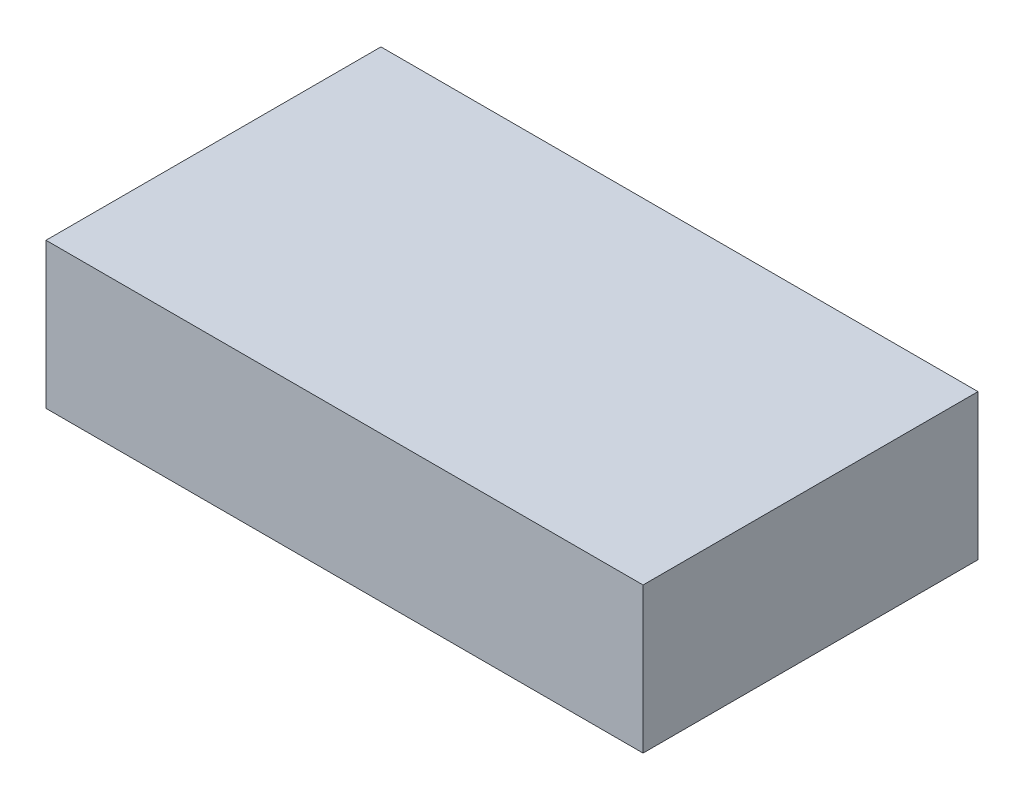
SolidWorks part; units mm, degrees
ref_plane "Front Plane" through (0, 0, 0) normal (0, 0, 1) x (1, 0, 0)
ref_plane "Top Plane" through (0, 0, 0) normal (0, 1, 0) x (1, 0, 0)
ref_plane "Right Plane" through (0, 0, 0) normal (1, 0, 0) x (0, 0, -1)
sketch "Sketch1" plane through (0, 0, 0) normal (0, 1, 0) x (1, 0, 0)
  line L1 (-102.5, -57.5) -> (102.5, -57.5)
  line L2 (-102.5, -57.5) -> (-102.5, 57.5)
  line L3 (-102.5, 57.5) -> (102.5, 57.5)
  line L4 (102.5, -57.5) -> (102.5, 57.5)
  line L5 (-102.5, -57.5) -> (102.5, 57.5) construction
  line L6 (-102.5, 57.5) -> (102.5, -57.5) construction
  point P0 (0, 0)
  dimension "D1" = 115
  dimension "D2" = 205
extrude "Boss-Extrude1" add sketch "Sketch1" along normal blind 50 contours L2 L1 L4 L3
sketch "Sketch2" plane through (0, 0, 0) normal (0, -1, 0) x (1, 0, 0)
  line L0 (-102.5, 57.5) -> (-102.5, -57.5) construction
  line L1 (70, -25) -> (-70, -25)
  line L2 (70, -25) -> (70, 25)
  line L3 (70, 25) -> (-70, 25)
  line L4 (-70, -25) -> (-70, 25)
  line L5 (70, -25) -> (-70, 25) construction
  line L6 (70, 25) -> (-70, -25) construction
  line L7 (-102.5, 57.5) -> (102.5, 57.5) construction
  point P0 (0, 0)
  dimension "D1" = 32.5
  dimension "D2" = 32.5
hole_wizard "M4 Clearance Hole1" positions "Sketch3" profile "Sketch5" hole size "M4" standard "ANSI Metric"
sketch "Sketch3" plane through (0, 0, 0) normal (0, -1, 0) x (-1, 0, 0)
  point P0 (70, -25)
  point P3 (-70, -25)
  point P6 (-70, 25)
  point P9 (70, 25)
sketch "Sketch5" plane through (-70, 0, 25) normal (1, 0, 0) x (0, 0, -1)
  line L0 (0, 0) -> (0, 6.3519)
  line L1 (0, 6.3519) -> (2.25, 5)
  line L2 (2.25, 5) -> (2.25, 0)
  line L5 (2.25, 0) -> (0, 0)
  line L10 (0, 6.3519) -> (-2.25, 5) construction
  line L11 (0, -6.35) -> (0, 107.95) construction
  dimension "Hole Dia." = 4.5
  dimension "Hole Depth" = 5
  dimension "Drill Angle" = 118
